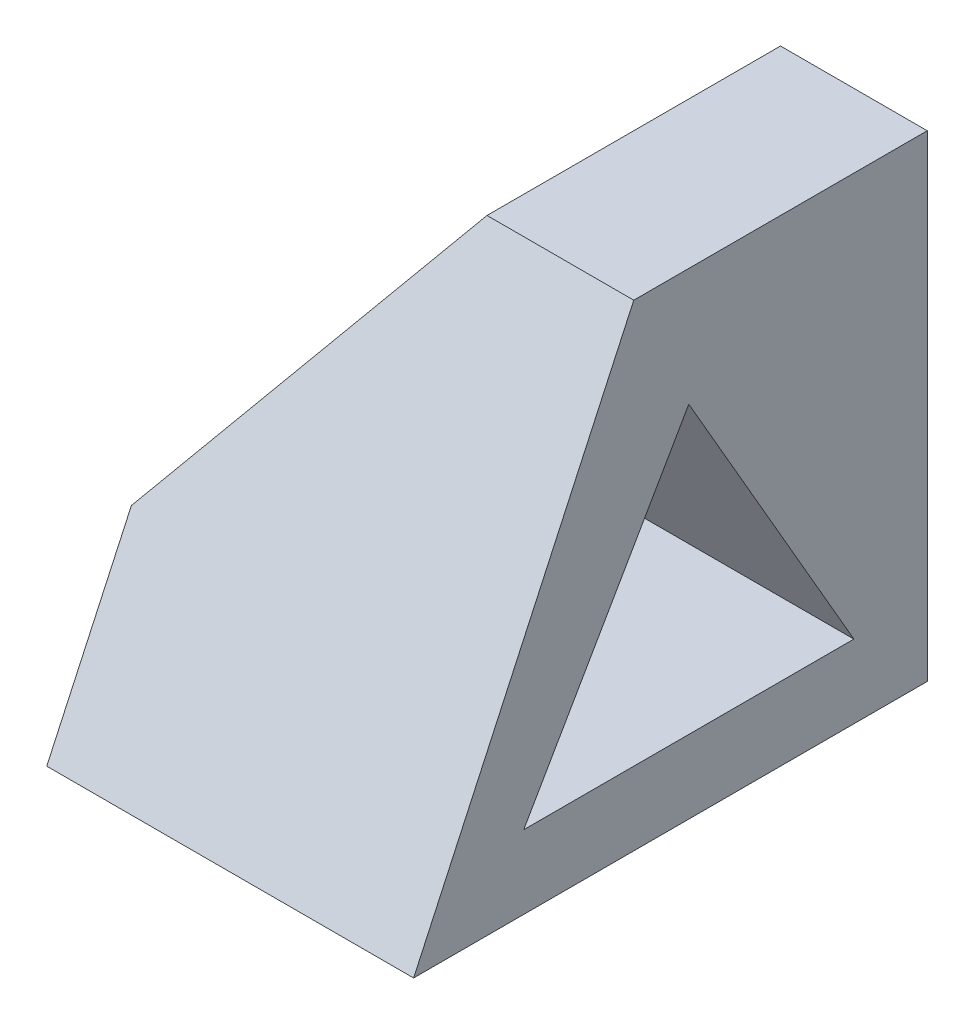
SolidWorks part; units mm, degrees
ref_plane "Front" through (0, 0, 0) normal (0, 0, 1) x (1, 0, 0)
ref_plane "Top" through (0, 0, 0) normal (0, 1, 0) x (1, 0, 0)
ref_plane "Right" through (0, 0, 0) normal (1, 0, 0) x (0, 0, -1)
sketch "Sketch1" plane through (0, 0, 0) normal (0, 0, 1) x (1, 0, 0)
  line L0 (30, 65) -> (0, 25)
  line L1 (0, 0) -> (50, 0)
  line L2 (0, 0) -> (0, 25)
  line L3 (30, 65) -> (50, 65)
  line L4 (50, 0) -> (50, 65)
  dimension "D1" = 50
  dimension "D2" = 65
  dimension "D3" = 20
  dimension "D4" = 40
extrude "Extrude1" add sketch "Sketch1" along normal blind 70
sketch "Sketch2" plane through (50, 0, 0) normal (1, 0, 0) x (0, 0, -1)
  line L0 (-70, 0) -> (-70, 65)
  line L1 (-70, 65) -> (-40, 65)
  line L2 (-70, 65) -> (0, 65) construction
  line L3 (-40, 65) -> (-70, 0)
  line L4 (-32.5, 48.9711) -> (-10, 10)
  line L5 (-10, 10) -> (-55, 10)
  line L6 (-55, 10) -> (-32.5, 48.9711)
  line L7 (-70, 0) -> (0, 0) construction
  line L8 (0, 0) -> (0, 65) construction
  dimension "D1" = 30
  dimension "D2" = 10
  dimension "D3" = 10
  dimension "D4" = 15
extrude "Cut-Extrude1" cut sketch "Sketch2" against normal through all
